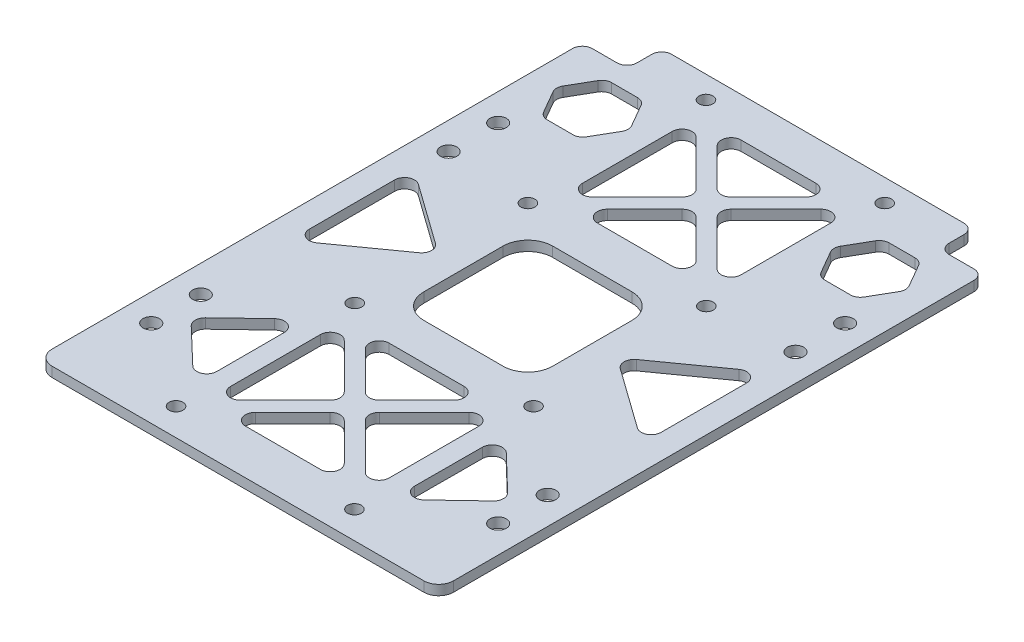
SolidWorks part; units mm, degrees
material "Thornel Mat VMA"
ref_plane "前视基准面" through (0, 0, 0) normal (0, 0, 1) x (1, 0, 0)
ref_plane "上视基准面" through (0, 0, 0) normal (0, 1, 0) x (1, 0, 0)
ref_plane "右视基准面" through (0, 0, 0) normal (1, 0, 0) x (0, 0, -1)
other "Configuration Table"
sketch "草图1" plane through (0, 0, 0) normal (0, 1, 0) x (1, 0, 0)
  line L1 (-40.5, -58.5) -> (40.5, -58.5)
  line L2 (-40.5, -58.5) -> (-40.5, 58.5)
  line L3 (-40.5, 58.5) -> (40.5, 58.5)
  line L4 (40.5, -58.5) -> (40.5, 58.5)
  line L5 (-40.5, -58.5) -> (40.5, 58.5) construction
  line L6 (-40.5, 58.5) -> (40.5, -58.5) construction
  point P0 (0, 0)
  dimension "D1" = 81
  dimension "D2" = 117
extrude "凸台-拉伸1" add sketch "草图1" along normal blind 2
fillet "圆角2" radius 3 4 edges at (40.5, 1, 58.5) (-40.5, 1, -58.5) (40.5, 1, -58.5) (-40.5, 1, 58.5)
sketch "草图2" plane through (0, 0, 0) normal (0, -1, 0) x (1, 0, 0)
  circle A0 centre (-18, 16.932) radius 1.4
  circle A1 centre (18.068, 16.932) radius 1.4
  circle A2 centre (-18, 53) radius 1.4
  circle A3 centre (17.9999, 53) radius 1.4
  circle A4 centre (-18, -18) radius 1.4
  circle A5 centre (18, -18) radius 1.4
  circle A6 centre (-18.0681, -54) radius 1.4
  circle A7 centre (17.9999, -54) radius 1.4
  circle A8 centre (-35, 41) radius 1.65
  circle A9 centre (35, 41) radius 1.65
  circle A10 centre (35, -19) radius 1.65
  circle A11 centre (-35, -19) radius 1.65
  circle A12 centre (-35, 31) radius 1.65
  circle A13 centre (-35, -29) radius 1.65
  circle A14 centre (35, -29) radius 1.65
  circle A15 centre (35, 31) radius 1.65
  point P44 (0, 0)
  point P45 (0, 0)
  point P46 (0, 0)
  point P47 (0, 0)
  point P48 (-35, 32.2647)
  dimension "D1" = 2.8
  dimension "D2" = 3.3
  dimension "D3" = 3.3
  dimension "D4" = 10
  dimension "D5" = 10
extrude "切除-拉伸1" cut sketch "草图2" against normal blind 10
sketch "草图4" plane through (0, 0, 0) normal (0, -1, 0) x (1, 0, 0)
  line L0 (31.5, -58.5) -> (31.5, -51.5)
  line L1 (37.5, -58.5) -> (-37.5, -58.5) construction
  line L2 (31.5, -51.5) -> (40.5, -51.5)
  line L3 (40.5, 55.5) -> (40.5, -55.5) construction
  line L4 (40.5, -51.5) -> (40.5, -55.5)
  line L5 (37.5, -58.5) -> (31.5, -58.5)
  line L6 (0, -58.5) -> (0, 58.5) construction
  line L7 (-37.5, 58.5) -> (37.5, 58.5) construction
  line L8 (-37.5, -58.5) -> (-31.5, -58.5)
  line L9 (-40.5, -51.5) -> (-40.5, -55.5)
  line L10 (-31.5, -51.5) -> (-40.5, -51.5)
  line L11 (-31.5, -58.5) -> (-31.5, -51.5)
  arc A0 (37.5, -58.5) -> (40.5, -55.5) centre (37.5, -55.5) ccw construction
  arc A1 (37.5, -58.5) -> (40.5, -55.5) centre (37.5, -55.5) ccw
  arc A2 (-37.5, -58.5) -> (-40.5, -55.5) centre (-37.5, -55.5) cw
  dimension "D1" = 7
  dimension "D2" = 9
extrude "切除-拉伸2" cut sketch "草图4" against normal blind 10
fillet "圆角3" radius 2 6 edges at (40.5, 1, -51.5) (-40.5, 1, -51.5) (-31.5, 1, -58.5) (31.5, 1, -58.5) (31.5, 1, -51.5) (-31.5, 1, -51.5)
sketch "草图5" plane through (0, 0, 0) normal (0, -1, 0) x (1, 0, 0)
  line L0 (-18, 53) -> (-18, 16.932) construction
  line L1 (-18, 16.932) -> (18.068, 16.932) construction
  line L2 (-12.3447, 49.466) -> (12.4127, 49.466)
  line L3 (17.534, 17.466) -> (-17.466, 17.466) construction
  line L4 (17.534, 17.466) -> (17.534, 52.466) construction
  line L5 (17.534, 52.466) -> (-17.466, 52.466) construction
  line L6 (-17.466, 17.466) -> (-17.466, 52.466) construction
  line L7 (17.534, 17.466) -> (-17.466, 52.466) construction
  line L8 (17.534, 52.466) -> (-17.466, 17.466) construction
  line L9 (12.4127, 49.466) -> (0.034, 37.0873)
  line L10 (0.034, 37.0873) -> (-12.3447, 49.466)
  line L11 (-15.966, 48.8447) -> (-15.966, 21.0873)
  line L12 (-15.966, 21.0873) -> (-2.0873, 34.966)
  line L13 (-2.0873, 34.966) -> (-15.966, 48.8447)
  line L14 (0.034, 34.966) -> (0.034, 52.466) construction
  line L15 (16.034, 48.8447) -> (16.034, 21.0873)
  line L16 (16.034, 21.0873) -> (2.1553, 34.966)
  line L17 (2.1553, 34.966) -> (16.034, 48.8447)
  line L18 (16.034, 34.966) -> (17.534, 34.966) construction
  line L19 (12.4127, 20.466) -> (0.034, 32.8447)
  line L20 (-12.3447, 20.466) -> (12.4127, 20.466)
  line L21 (0.034, 32.8447) -> (-12.3447, 20.466)
  line L22 (18.068, 16.932) -> (18, -18) construction
  line L23 (18.034, -0.534) -> (40.5, -0.534) construction
  line L24 (40.5, 55.5) -> (40.5, -49.5) construction
  line L25 (12.4127, -21.534) -> (0.034, -33.9127)
  line L26 (16.034, -22.1554) -> (2.1553, -36.034)
  line L27 (16.034, -49.9127) -> (16.034, -22.1554)
  line L28 (2.1553, -36.034) -> (16.034, -49.9127)
  line L29 (12.4127, -50.534) -> (0.034, -38.1554)
  line L30 (-12.3447, -50.534) -> (12.4127, -50.534)
  line L31 (0.034, -38.1554) -> (-12.3447, -50.534)
  line L32 (-2.0873, -36.034) -> (-15.966, -49.9127)
  line L33 (-15.966, -49.9127) -> (-15.966, -22.1554)
  line L34 (-15.966, -22.1554) -> (-2.0873, -36.034)
  line L35 (0.034, -33.9127) -> (-12.3447, -21.534)
  line L36 (-12.3447, -21.534) -> (12.4127, -21.534)
  point P4 (0.034, 34.966)
  point P7 (0.034, 16.932)
  point P9 (-18, 34.966)
  point P10 (0.034, 34.966)
  dimension "D1" = 35
  dimension "D2" = 35
  dimension "D3" = 3
  dimension "D4" = 3
  dimension "D5" = 3
  dimension "D6" = 3
extrude "切除-拉伸3" cut sketch "草图5" against normal blind 10
fillet "圆角4" radius 2 24 edges at (12.4127, 1, 49.466) (0.034, 1, 37.0873) (-12.3447, 1, 49.466) (0.034, 1, -38.1554) (12.4127, 1, -50.534) (-12.3447, 1, -50.534) (2.1553, 1, -36.034) (16.034, 1, -22.1554) (16.034, 1, -49.9127) (-15.966, 1, -49.9127) (-15.966, 1, -22.1554) (-2.0873, 1, -36.034) (-15.966, 1, 21.0873) (-15.966, 1, 48.8447) (-2.0873, 1, 34.966) (16.034, 1, 21.0873) (2.1553, 1, 34.966) (0.034, 1, 32.8447) (12.4127, 1, 20.466) (-12.3447, 1, 20.466) (0.034, 1, -33.9127) (-12.3447, 1, -21.534) (12.4127, 1, -21.534) (16.034, 1, 48.8447)
sketch "草图6" plane through (0, 0, 0) normal (0, -1, 0) x (1, 0, 0)
  line L1 (-13, -13) -> (13, -13)
  line L2 (-13, -13) -> (-13, 13)
  line L3 (-13, 13) -> (13, 13)
  line L4 (13, -13) -> (13, 13)
  line L5 (-13, -13) -> (13, 13) construction
  line L6 (-13, 13) -> (13, -13) construction
  point P0 (0, 0)
  dimension "D1" = 26
  dimension "D2" = 26
extrude "切除-拉伸4" cut sketch "草图6" against normal blind 10
fillet "圆角5" radius 5 4 edges at (-13, 1, -13) (-13, 1, 13) (13, 1, -13) (13, 1, 13)
sketch "草图7" plane through (0, 0, 0) normal (0, -1, 0) x (1, 0, 0)
  line L0 (35.5, 12.5) -> (35.5, -12.5)
  line L1 (35.5, -12.5) -> (18, 0)
  line L2 (18, 0) -> (35.5, 12.5)
  line L3 (40.5, 55.5) -> (40.5, -49.5) construction
  line L4 (35.5, 0) -> (18, 0) construction
  line L5 (13, -8) -> (13, 8) construction
  point P8 (0, 0)
  point P9 (13, 0)
  dimension "D1" = 5
  dimension "D2" = 5
  dimension "D3" = 25
extrude "切除-拉伸5" cut sketch "草图7" against normal blind 10
fillet "圆角6" radius 2 3 edges at (35.5, 1, -12.5) (18, 1, 0) (35.5, 1, 12.5)
mirror "镜向1" about plane through (0, 0, 0) normal (1, 0, 0) of "切除-拉伸5", "圆角6"
sketch "草图8" plane through (0, 0, 0) normal (0, -1, 0) x (1, 0, 0)
  line L0 (38.5, -51.5) -> (33.5, -51.5) construction
  line L1 (-24.2417, -34.5) -> (-31.7472, -34.5)
  line L2 (-31.7472, -34.5) -> (-35.5, -41)
  line L3 (-35.5, -41) -> (-31.7472, -47.5)
  line L4 (-31.7472, -47.5) -> (-24.2417, -47.5)
  line L5 (-24.2417, -47.5) -> (-20.4889, -41)
  line L6 (-20.4889, -41) -> (-24.2417, -34.5)
  line L7 (31.7472, -34.5) -> (24.2417, -34.5)
  line L8 (24.2417, -34.5) -> (20.4889, -41)
  line L9 (20.4889, -41) -> (24.2417, -47.5)
  line L10 (24.2417, -47.5) -> (31.7472, -47.5)
  line L11 (31.7472, -47.5) -> (35.5, -41)
  line L12 (35.5, -41) -> (31.7472, -34.5)
  line L13 (40.5, 55.5) -> (40.5, -49.5) construction
  line L14 (-40.5, -49.5) -> (-40.5, 55.5) construction
  line L15 (-33.5, -51.5) -> (-38.5, -51.5) construction
  circle A0 centre (-27.9944, -41) radius 6.5 construction
  circle A1 centre (27.9944, -41) radius 6.5 construction
  dimension "D1" = 13
  dimension "D2" = 4
  dimension "D3" = 5
  dimension "D4" = 5
  dimension "D5" = 4
extrude "切除-拉伸6" cut sketch "草图8" against normal blind 10
sketch "草图9" plane through (0, 0, 0) normal (0, -1, 0) x (1, 0, 0)
  line L0 (-19.966, 47.5) -> (-19.966, 24.5)
  line L1 (-19.966, 24.5) -> (-32, 36)
  line L2 (-32, 36) -> (-19.966, 47.5)
  line L3 (-15.966, 44.0163) -> (-15.966, 25.9157) construction
  line L4 (-35, 32.65) -> (-35, 39.35) construction
  line L5 (0.034, 37.9157) -> (0, 58.5) construction
  line L6 (-37.5, 58.5) -> (37.5, 58.5) construction
  line L7 (35.0852, 32.7658) -> (35.0631, 39.4657) construction
  line L8 (32.0742, 36.1058) -> (20.0022, 47.566)
  line L9 (20.0782, 24.5661) -> (32.0742, 36.1058)
  line L10 (20.0022, 47.566) -> (20.0782, 24.5661)
  circle A0 centre (-35, 31) radius 1.65 construction
  circle A1 centre (-35, 41) radius 1.65 construction
  arc A2 (-1.3802, 38.5015) -> (1.4482, 38.5015) centre (0.034, 39.9157) ccw construction
  point P5 (-35, 36)
  dimension "D1" = 4
  dimension "D2" = 3
  dimension "D3" = 23
extrude "切除-拉伸7" cut sketch "草图9" against normal blind 10
fillet "圆角7" radius 2 18 edges at (31.7472, 1, -47.5) (24.2417, 1, -47.5) (20.4889, 1, -41) (24.2417, 1, -34.5) (31.7472, 1, -34.5) (35.5, 1, -41) (-24.2417, 1, -47.5) (-31.7472, 1, -47.5) (-35.5, 1, -41) (-31.7472, 1, -34.5) (-24.2417, 1, -34.5) (-20.4889, 1, -41) (20.0022, 1, 47.566) (32.0742, 1, 36.1058) (20.0782, 1, 24.5661) (-19.966, 1, 24.5) (-19.966, 1, 47.5) (-32, 1, 36)
